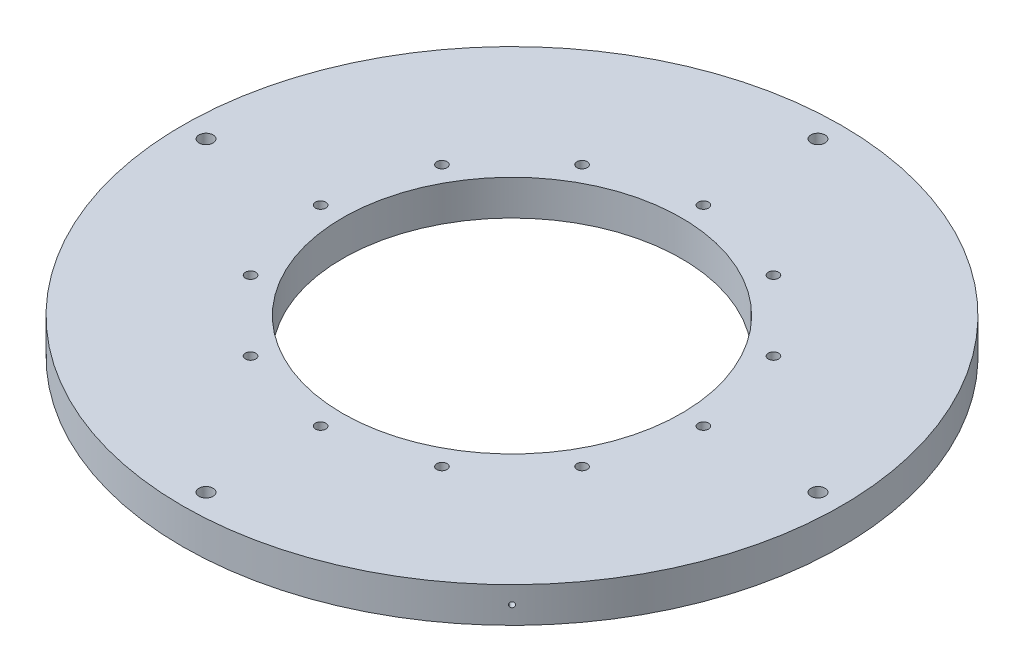
SolidWorks part; units mm, degrees
material "6061-T6 (SS)"
ref_plane "Front Plane" through (0, 0, 0) normal (0, 0, 1) x (1, 0, 0)
ref_plane "Top Plane" through (0, 0, 0) normal (0, 1, 0) x (1, 0, 0)
ref_plane "Right Plane" through (0, 0, 0) normal (1, 0, 0) x (0, 0, -1)
sketch "Sketch1" plane through (0, 0, 0) normal (0, 1, 0) x (1, 0, 0)
  circle A0 centre (0, 0) radius 88.9
  dimension "D1" = 177.8
extrude "Boss-Extrude1" add sketch "Sketch1" along normal blind 9.525
sketch "Sketch2" plane through (0, 9.525, 0) normal (0, 1, 0) x (1, 0, 0)
  circle A0 centre (0, 0) radius 45.72
extrude "Cut-Extrude1" cut sketch "Sketch2" against normal blind 12.7
sketch "Sketch3" plane through (0, 9.525, 0) normal (0, 1, 0) x (1, 0, 0)
  line L0 (0, 0) -> (0, 131.3286) construction
  circle A0 centre (0, 51.6382) radius 1.397
  point P0 (0, 51.6382)
  dimension "D2" = 2.794
  dimension "D1" = 51.6382
extrude "Cut-Extrude2" cut sketch "Sketch3" against normal blind 12.7
pattern_circular "CirPattern1" count 12 over 360 about axis through (0, 0, 0) along (0, 1, 0) of "Cut-Extrude2"
sketch "Sketch4" plane through (0, 9.525, 0) normal (0, 1, 0) x (1, 0, 0)
  line L0 (0, 0) -> (0, 115.2639) construction
  circle A0 centre (0, 82.55) radius 1.905
  dimension "D1" = 3.81
  dimension "D2" = 82.55
extrude "Cut-Extrude3" cut sketch "Sketch4" against normal blind 12.7
pattern_circular "CirPattern2" count 4 over 360 about axis through (0, 0, 0) along (0, 1, 0) of "Cut-Extrude3"
ref_plane "Plane3" through (-62.8618, 0, -62.8618) normal (-0.7071, 0, -0.7071) x (0, -1, 0)
sketch "Sketch10" plane through (-62.8618, 0, -62.8618) normal (-0.7071, 0, -0.7071) x (0, -1, 0)
  line L0 (0, 0) -> (-9.652, 0) construction
  circle A1 centre (-4.826, 0) radius 0.6985
  dimension "D2" = 1.397
  dimension "D1" = 9.652
extrude "Cut-Extrude5" cut sketch "Sketch10" against normal blind 3.175
pattern_circular "CirPattern5" count 4 over 360 about axis through (0, 0, 0) along (0, 1, 0) of "Cut-Extrude5"
